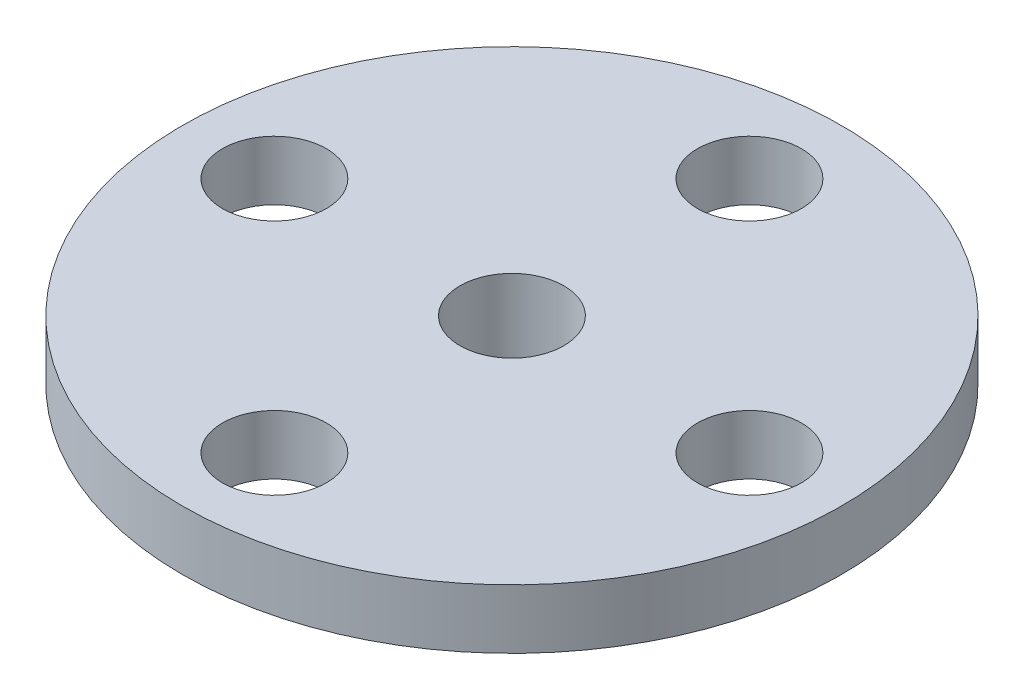
SolidWorks part; units mm, degrees
material "6061 Alloy"
ref_plane "Front Plane" through (0, 0, 0) normal (0, 0, 1) x (1, 0, 0)
ref_plane "Top Plane" through (0, 0, 0) normal (0, 1, 0) x (1, 0, 0)
ref_plane "Right Plane" through (0, 0, 0) normal (1, 0, 0) x (0, 0, -1)
sketch "Sketch1" plane through (0, 0, 0) normal (0, 1, 0) x (1, 0, 0)
  circle A0 centre (0, 0) radius 11.1
  dimension "D1" = 22.2
extrude "Extrude1" add sketch "Sketch1" along normal blind 2
sketch "Sketch2" plane through (0, 2, 0) normal (0, 1, 0) x (1, 0, 0)
  circle A0 centre (0, 8) radius 1.75
  circle A1 centre (8, 0) radius 1.75
  circle A2 centre (0, -8) radius 1.75
  circle A3 centre (-8, 0) radius 1.75
  dimension "D1" = 3.5
  dimension "D2" = 3.5
  dimension "D3" = 3.5
  dimension "D4" = 3.5
  dimension "D5" = 8
  dimension "D6" = 8
  dimension "D7" = 8
  dimension "D8" = 8
extrude "Cut-Extrude1" cut sketch "Sketch2" against normal through all
sketch "Sketch3" plane through (0, 0, 0) normal (0, -1, 0) x (1, 0, 0)
  circle A0 centre (0, 0) radius 4.4
  dimension "D1" = 8.8
extrude "Extrude2" add sketch "Sketch3" along normal blind 4.2
sketch "Sketch4" plane through (0, -4.2, 0) normal (0, -1, 0) x (1, 0, 0)
  circle A0 centre (0, 0) radius 2.85
  dimension "D1" = 5.7
extrude "Cut-Extrude2" cut sketch "Sketch4" against normal blind 3
sketch "Sketch5" plane through (0, -1.2, 0) normal (0, -1, 0) x (1, 0, 0)
  circle A0 centre (0, 0) radius 1.75
  dimension "D1" = 3.5
extrude "Cut-Extrude3" cut sketch "Sketch5" against normal through all
